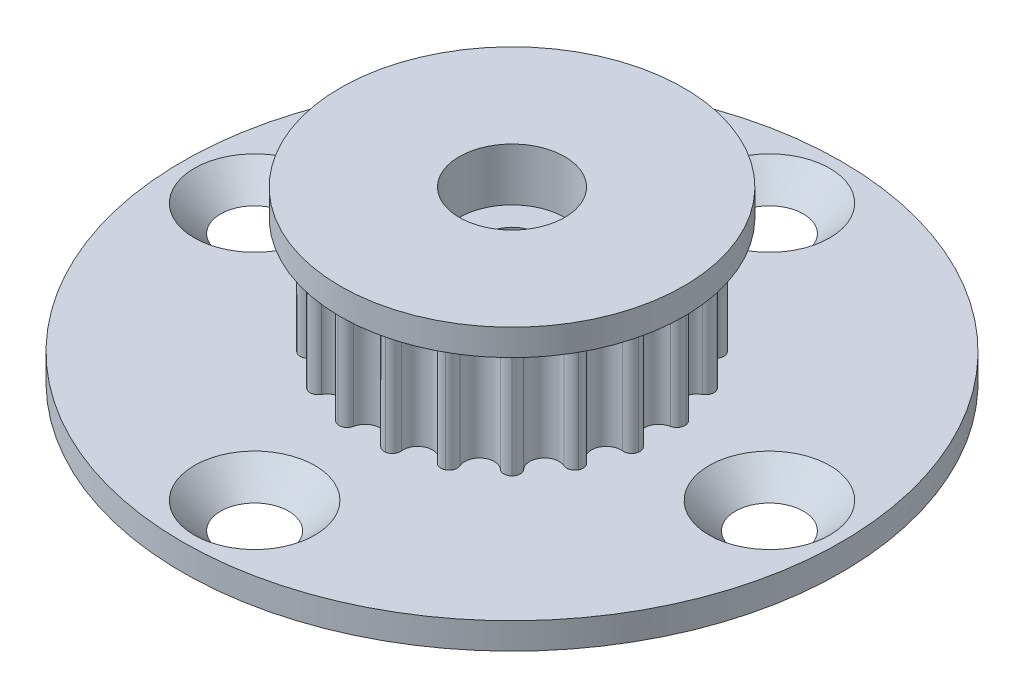
SolidWorks part; units mm, degrees
ref_plane "Front Plane" through (0, 0, 0) normal (0, 0, 1) x (1, 0, 0)
ref_plane "Top Plane" through (0, 0, 0) normal (0, 1, 0) x (1, 0, 0)
ref_plane "Right Plane" through (0, 0, 0) normal (1, 0, 0) x (0, 0, -1)
sketch "Sketch1" plane through (0, 0, 0) normal (0, 1, 0) x (1, 0, 0)
  line L0 (0, 0) -> (0, 9.1676) construction
  line L1 (0, 0) -> (2.731, 8.405) construction
  circle A0 centre (0, 0) radius 9.1676 construction
  circle A1 centre (0, 0) radius 7.9476 construction
  circle A2 centre (0, 8.8376) radius 0.89 construction
  circle A5 centre (2.731, 8.405) radius 0.89 construction
  arc A6 (0, 7.9476) -> (0.8721, 8.6598) centre (0, 8.8376) ccw
  arc A7 (0.8721, 8.6598) -> (1.4405, 9.0537) centre (1.362, 8.5599) cw
  arc A8 (1.4277, 9.0557) -> (1.8466, 8.5054) centre (1.3498, 8.5618) cw
  arc A9 (2.4559, 7.5586) -> (1.8466, 8.5054) centre (2.731, 8.405) cw
  arc A10 (1.4405, 9.0537) -> (1.4277, 9.0557) centre (0, 0) cw
  arc A11 (0, 7.9476) -> (2.4559, 7.5586) centre (0, 0) ccw
  dimension "D1" = 18.3352
  dimension "D3" = 1.78
  dimension "D4" = 0.5
  dimension "D2" = 1.22
  dimension "D5" = 18
extrude "Boss-Extrude1" add sketch "Sketch1" along normal mid plane 7.112 contours A6 A11 A9 A8 A7
ref_axis "Axis1" through (0, 3.3, 0) along (0, -1, 0)
pattern_circular "CirPattern1" count 20 over 360 about axis through (0, 0, 0) along (0, 1, 0) of "Boss-Extrude1"
sketch "Sketch2" plane through (0, 0, 0) normal (1, 0, 0) x (0, 0, -1)
  line L10 (0, 3.5) -> (10.3423, 3.5) construction
  line L11 (0, 3.5) -> (0, 5.0875) construction
  line L12 (0, 5.0875) -> (10.3423, 5.0875) construction
  line L15 (10.3423, 3.5) -> (10.3423, 5.0875) construction
  line L20 (0, 3.3) -> (0, -3.3) construction
  line L22 (10.3423, 5.0875) -> (0, 5.0875)
  line L23 (10.3423, 5.0875) -> (10.3423, 3.5)
  line L24 (10.3423, 3.5) -> (0, 3.5)
  line L25 (0, 5.0875) -> (0, 3.5)
  dimension "D1" = 1.5875
  dimension "D2" = 10.3423
  dimension "D3" = 3.5
revolve "Revolve3" add sketch "Sketch2" angle 360 about axis through (0, 3.3, 0) along (0, -1, 0)
mirror "Mirror1" about plane through (0, 0, 0) normal (0, 1, 0) of "Revolve3"
sketch "Sketch9" plane through (0, -5.0875, 0) normal (0, -1, 0) x (1, 0, 0)
  circle A0 centre (0, 0) radius 19.8438
  circle A1 centre (0, 0) radius 1.5
  dimension "D1" = 3
  dimension "D2" = 39.6875
extrude "Boss-Extrude2" add sketch "Sketch9" against normal up to surface (1.5875 mm away) up to face at (0, -3.5, 0)
sketch "Sketch3" plane through (0, 0, 0) normal (0, 1, 0) x (1, 0, 0)
  circle A0 centre (-15.5, 0) radius 1.7462
  circle A3 centre (0, 15.5) radius 1.7462
  circle A4 centre (15.5, 0) radius 1.7463
  circle A5 centre (0, -15.5) radius 1.7462
  dimension "D3" = 3.4925
  dimension "D1" = 15.5
  dimension "D4" = 4
extrude "Cut-Extrude1" cut sketch "Sketch3" against normal through all both and the other way through all
ref_axis "Axis2" through (-15.5, -5.0875, 0) along (0, 1, 0)
sketch "Sketch6" plane through (0, 0, 0) normal (0, 0, 1) x (1, 0, 0)
  line L0 (-19.1322, -3.5) -> (-11.8678, -3.5) construction
  line L1 (-13.7538, -3.5) -> (-17.2462, -3.5) construction
  line L2 (-11.8678, -3.5) -> (-15.5, -7.1322)
  line L3 (-15.5, -7.1322) -> (-19.1322, -3.5) construction
  line L4 (-18.548, -4.0842) -> (-12.452, -4.0842) construction
  line L5 (-17.2462, -3.998) -> (-13.7538, -3.998) construction
  line L8 (-15.5, -7.1322) -> (-15.5, -3.5)
  line L9 (-15.5, -3.5) -> (-11.8678, -3.5)
  line L10 (-15.5, -5.0875) -> (-15.5, -3.5) construction
  line L12 (-17.2462, -3.5) -> (-17.2462, -5.0875) construction
  line L13 (-13.7538, -5.0875) -> (-13.7538, -3.5) construction
  point P2 (-15.5, -3.998)
  dimension "D1" = 6.096
  dimension "D2" = 0.5842
revolve "Cut-Revolve2" cut sketch "Sketch6" angle 360 about axis through (-15.5, -5.0875, 0) along (0, 1, 0)
pattern_circular "CirPattern2" count 4 over 360 about axis through (0, 0, 0) along (0, 1, 0) of "Cut-Revolve2"
sketch "Sketch12" plane through (0, 5.0875, 0) normal (0, 1, 0) x (1, 0, 0)
  circle A0 centre (0, 0) radius 3.175
  dimension "D1" = 6.35
extrude "Cut-Extrude2" cut sketch "Sketch12" against normal blind 3.175 from surface at 0 starting at face at (0, 5.0875, 10.3423)
sketch "Sketch13" plane through (0, 1.9125, 0) normal (0, 1, 0) x (1, 0, 0)
  circle A0 centre (0, 0) radius 1.525
  dimension "D1" = 3.05
extrude "Cut-Extrude4" cut sketch "Sketch13" against normal through all contours A0
equation "\"TEETH_NUM\" = 20"
equation "\"TOOTH_PITCH\"= 3mm"
equation "\"PITCH_LINE_OFFSET\"= .015in"
equation "\"DIAMETER_PER_GROOVE\"= \"OUTSIDE_DIAMETER\" / \"TEETH_NUM\" * 1in"
equation "\"PITCH_DIAMETER\"= ( ( \"TEETH_NUM\" * 3 - 1.31 ) / 3.1415 + .415 ) * 1mm"
equation "\"OUTSIDE_DIAMETER\"= \"PITCH_DIAMETER\" - \"PITCH_LINE_OFFSET\" * 2"
equation "\"D1@Sketch1\"=\"OUTSIDE_DIAMETER\""
equation "\"TOOTH_HEIGHT\"= 1.22mm"
equation "\"D2@Sketch1\"=\"TOOTH_HEIGHT\""
equation "\"TOOTH_DIAMETER\"= 1.78mm"
equation "\"INTERNAL_RADIUS\"= .5mm"
equation "\"D3@Sketch1\"=\"TOOTH_DIAMETER\""
equation "\"D5@Sketch1\"=360 / \"TEETH_NUM\""
equation "\"D4@Sketch1\"=\"INTERNAL_RADIUS\""
equation "\"D1@CirPattern1\"=\"TEETH_NUM\""
equation "\"BELT_GAP\"= 7mm"
equation "\"D2@Sketch2\"=\"PITCH_DIAMETER\"/2+1/32"
equation "\"D3@Sketch2\"=\"BELT_GAP\"/2"
